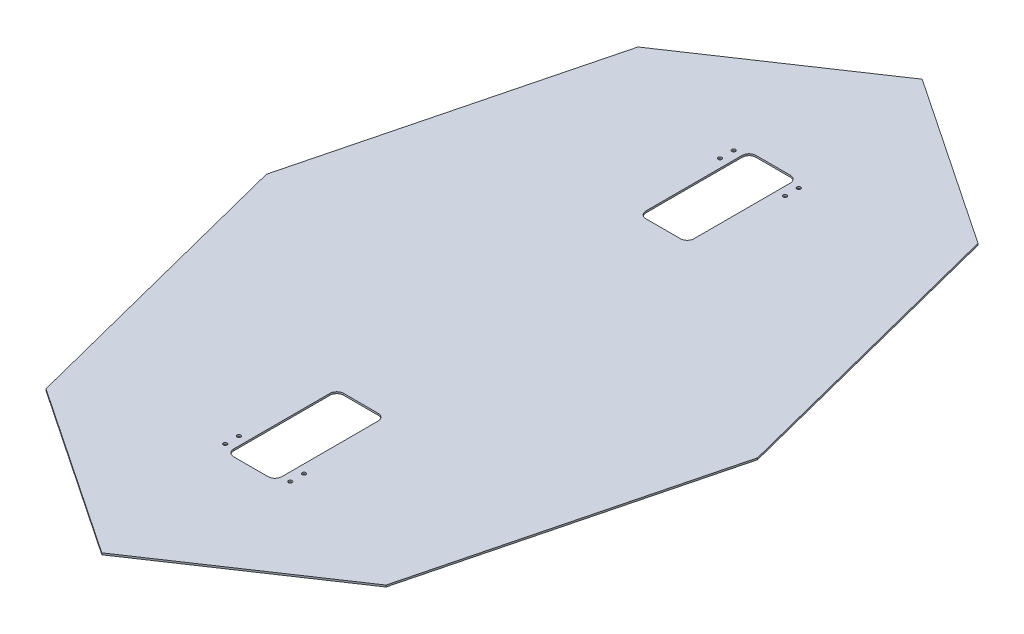
SolidWorks part; units mm, degrees
material "AISI 1020"
ref_plane "Front Plane" through (0, 0, 0) normal (0, 0, 1) x (1, 0, 0)
ref_plane "Top Plane" through (0, 0, 0) normal (0, 1, 0) x (1, 0, 0)
ref_plane "Right Plane" through (0, 0, 0) normal (1, 0, 0) x (0, 0, -1)
sketch "Sketch1" plane through (0, 0, 0) normal (0, 1, 0) x (1, 0, 0)
  line L0 (0, -549.0794) -> (0, 549.0794) construction
  line L1 (-314.2347, 547.1196) -> (-453.9232, 0)
  line L2 (-314.2347, -547.1196) -> (-453.9232, 0)
  line L3 (0, -758.1753) -> (-314.2347, -547.1196)
  line L4 (314.2347, -547.1196) -> (0, -758.1753)
  line L5 (317.0112, 0) -> (-317.0112, 0) construction
  line L6 (314.2347, -547.1196) -> (453.9232, 0)
  line L7 (453.9232, 0) -> (314.2347, 547.1196)
  line L8 (314.2347, 547.1196) -> (0, 758.1753)
  line L9 (-314.2347, 547.1196) -> (0, 758.1753)
  line L23 (-317.0112, -549.0794) -> (-457.2, 0) construction
  line L24 (0, -762) -> (-317.0112, -549.0794) construction
  line L25 (317.0112, -549.0794) -> (0, -762) construction
  line L26 (317.0112, -549.0794) -> (457.2, 0) construction
  line L27 (457.2, 0) -> (317.0112, 549.0794) construction
  line L28 (317.0112, 549.0794) -> (0, 762) construction
  line L29 (-317.0112, 549.0794) -> (0, 762) construction
  line L30 (-317.0112, 549.0794) -> (-457.2, 0) construction
  line L39 (-317.0112, -549.0794) -> (317.0112, -549.0794) construction
  line L40 (-317.0112, -549.0794) -> (-317.0112, 549.0794) construction
  line L41 (-317.0112, 549.0794) -> (317.0112, 549.0794) construction
  line L42 (317.0112, -549.0794) -> (317.0112, 549.0794) construction
  line L43 (-317.0112, -549.0794) -> (317.0112, 549.0794) construction
  line L44 (-317.0112, 549.0794) -> (317.0112, -549.0794) construction
  ellipse E0 centre (0, 0) end of major axis (0, 762) minor radius 457.2 construction
  point P50 (0, 0)
  dimension "D1" = 3.175
  dimension "D3" = 30
  dimension "D8" = 762
  dimension "D9" = 457.2
extrude "Boss-Extrude1" add sketch "Sketch1" along normal mid plane 3.175
sketch "Sketch2" plane through (0, 0, 0) normal (0, 1, 0) x (1, 0, 0)
  line L1 (82.55, -457.2) -> (-82.55, -457.2) construction
  line L2 (82.55, -457.2) -> (82.55, 457.2) construction
  line L3 (82.55, 457.2) -> (-82.55, 457.2) construction
  line L4 (-82.55, -457.2) -> (-82.55, 457.2) construction
  line L5 (0, 457.2) -> (0, -457.2) construction
  line L6 (60.198, 444.5) -> (-60.198, 444.5) construction
  line L7 (-44.45, 279.4) -> (44.45, 279.4)
  line L8 (-44.45, 279.4) -> (-44.45, 482.6)
  line L9 (-44.45, 482.6) -> (44.45, 482.6)
  line L10 (44.45, 279.4) -> (44.45, 482.6)
  line L11 (60.198, 444.5) -> (60.198, 469.9) construction
  line L17 (-82.55, 0) -> (82.55, 0) construction
  line L18 (60.198, 469.9) -> (-60.198, 469.9) construction
  line L19 (-60.198, 444.5) -> (-60.198, 469.9) construction
  line L22 (60.198, 444.5) -> (-60.198, 469.9) construction
  line L23 (60.198, 469.9) -> (-60.198, 444.5) construction
  circle A0 centre (-60.198, 469.9) radius 3.429
  circle A1 centre (-60.198, 444.5) radius 3.429
  circle A2 centre (60.198, 444.5) radius 3.429
  circle A3 centre (60.198, 469.9) radius 3.429
  point P0 (0, 0)
  point P11 (0, 482.6)
  point P36 (0, 0)
  dimension "D7" = 6.858
  dimension "D1" = 165.1
  dimension "D2" = 914.4
  dimension "D3" = 88.9
  dimension "D4" = 177.8
  dimension "D6" = 25.4
  dimension "D8" = 25.4
  dimension "D10" = 120.396
extrude "Cut-Extrude1" cut sketch "Sketch2" against normal through all both and the other way through all
fillet "Fillet1" radius 12.7 4 edges at (-44.45, 0, -482.6) (44.45, 0, -482.6) (44.45, 0, -279.4) (-44.45, 0, -279.4)
sketch "Sketch4" plane through (0, 1.5875, 0) normal (0, 1, 0) x (1, 0, 0)
  line L1 (149.225, -66.675) -> (257.175, -66.675) construction
  line L2 (149.225, -66.675) -> (149.225, -136.525) construction
  line L3 (149.225, -136.525) -> (257.175, -136.525) construction
  line L4 (257.175, -66.675) -> (257.175, -136.525) construction
  line L5 (149.225, -66.675) -> (257.175, -136.525) construction
  line L6 (149.225, -136.525) -> (257.175, -66.675) construction
  line L7 (152.4, 254) -> (254, 254) construction
  line L8 (152.4, 254) -> (152.4, 152.4) construction
  line L9 (152.4, 152.4) -> (254, 152.4) construction
  line L10 (254, 254) -> (254, 152.4) construction
  line L11 (152.4, 254) -> (254, 152.4) construction
  line L12 (152.4, 152.4) -> (254, 254) construction
  circle A0 centre (257.175, -66.675) radius 3.175
  circle A1 centre (149.225, -66.675) radius 3.175
  circle A2 centre (149.225, -136.525) radius 3.175
  circle A3 centre (257.175, -136.525) radius 3.175
  circle A4 centre (152.4, 254) radius 3.175
  circle A5 centre (254, 254) radius 3.175
  circle A6 centre (254, 152.4) radius 3.175
  circle A7 centre (152.4, 152.4) radius 3.175
  point P0 (203.2, -101.6)
  point P9 (203.2, 203.2)
  dimension "D1" = 6.35
  dimension "D8" = 6.35
  dimension "D2" = 107.95
  dimension "D3" = 69.85
  dimension "D4" = 101.6
  dimension "D5" = 203.2
  dimension "D6" = 101.6
  dimension "D7" = 304.8
extrude "Cut-Extrude3" [suppressed] cut sketch "Sketch4" against normal up to next
mirror "Mirror1" about plane through (0, 0, 0) normal (0, 0, 1) of "Fillet1", "Cut-Extrude1"
